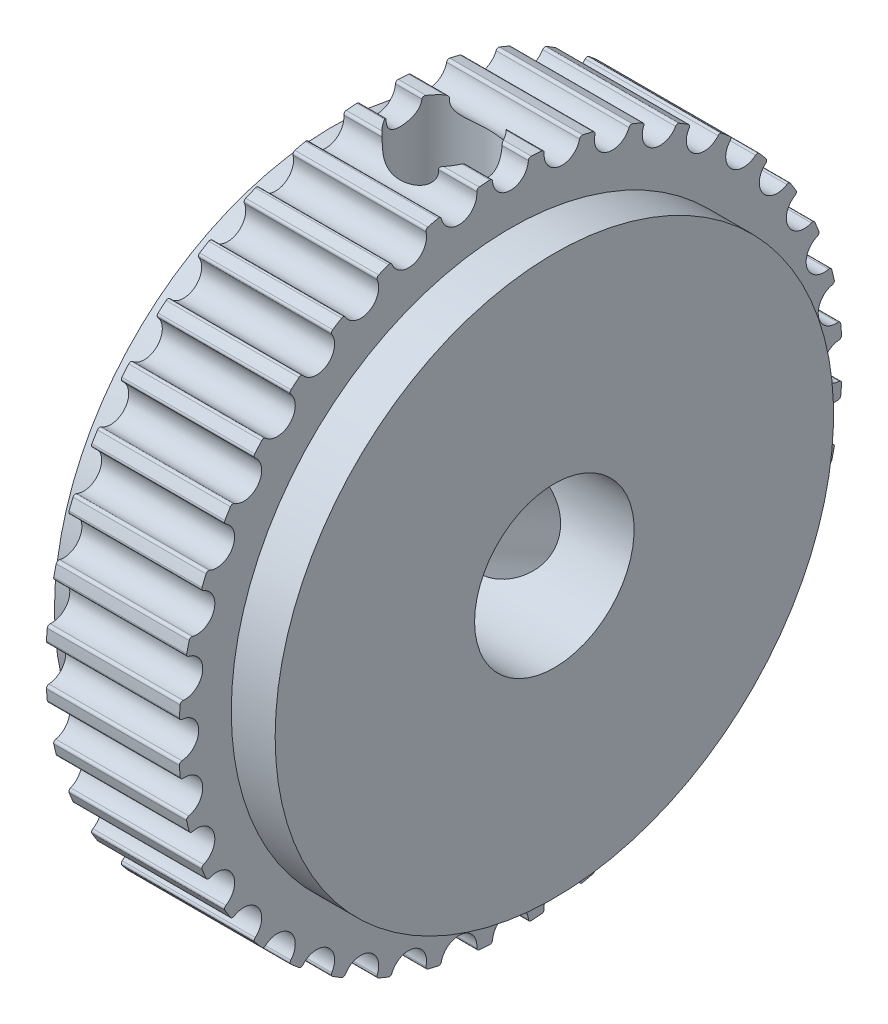
SolidWorks part; units mm, degrees
ref_plane "Front Plane" through (0, 0, 0) normal (0, 0, 1) x (1, 0, 0)
ref_plane "Top Plane" through (0, 0, 0) normal (0, 1, 0) x (1, 0, 0)
ref_plane "Right Plane" through (0, 0, 0) normal (1, 0, 0) x (0, 0, -1)
sketch "Sketch1" plane through (0, 0, 0) normal (0, 0, 1) x (1, 0, 0)
  line L0 (1.65, 12.73) -> (6.65, 12.73) construction
  line L1 (1.65, 12.475) -> (6.65, 12.475)
  line L2 (0, 10.5) -> (0, 3)
  line L4 (8.3, 10.5) -> (8.3, 3)
  line L5 (0, 3) -> (8.3, 3)
  line L6 (0, 0) -> (8.3, 0) construction
  line L8 (1.65, 10.5) -> (0, 10.5)
  line L9 (6.65, 10.5) -> (6.65, 12.475)
  line L10 (8.3, 10.5) -> (6.65, 10.5)
  line L13 (1.65, 10.5) -> (1.65, 12.475)
  dimension "D2" = 1.65
  dimension "D1" = 1.65
  dimension "O.D." = 24.95
  dimension "W" = 8.3
  dimension "E" = 21
  dimension "P.D." = 25.46
  dimension "A" = 5
  dimension "P" = 6
revolve "Revolve1" add sketch "Sketch1" angle 360 about L6
sketch "Sketch2" plane through (1.65, 0, 0) normal (1, 0, 0) x (0, 0, -1)
  line L0 (0, 0) -> (0, 12.475) construction
  circle A0 centre (0, 0) radius 12.475 construction
  circle A1 centre (0, 0) radius 12.475 construction
  arc A2 (0.6726, 12.4569) -> (-0.6726, 12.4569) centre (0, 0) ccw
  arc A3 (-0.6726, 12.4569) -> (0.6726, 12.4569) centre (0, 12.4) ccw
  circle A6 centre (0, 0) radius 11.725 construction
  circle A7 centre (0, 0) radius 12.729 construction
  dimension "MSM_3" = 0.675
  dimension "MSM_2" = 0.254
  dimension "MSM_1" = 0.75
extrude "Cut-Extrude1" cut sketch "Sketch2" along normal through all
fillet "Fillet1" radius 0.1 2 edges at (4.15, 12.4569, -0.6726) (4.15, 12.4569, 0.6726)
pattern_circular "CirPattern1" count 40 over 360 about axis through (0, 0, 0) along (1, 0, 0) of "Cut-Extrude1", "Fillet1"
ref_plane "Plane1" through (0, 12.475, 0) normal (0, 1, 0) x (1, 0, 0)
hole_wizard "Tapped Hole1" positions "Sketch4" profile "Sketch3" tap size "M4x0.7" standard "JIS"
sketch "Sketch4" plane through (-11.0915, 12.475, -15.1051) normal (0, 1, 0) x (1, 0, 0)
  line L0 (11.0915, -4.6051) -> (11.0915, -25.6051) construction
  line L1 (15.2415, -15.1051) -> (11.0915, -15.1051) construction
  point P0 (15.2415, -15.1051)
  dimension "D1" = 4.15
sketch "Sketch3" plane through (4.15, 12.475, 0) normal (1, 0, 0) x (0, 0, 1)
  line L0 (0, 0) -> (0, 9.475)
  line L1 (0, 9.475) -> (1.65, 9.475)
  line L2 (1.65, 9.475) -> (1.65, 0)
  line L5 (1.65, 0) -> (0, 0)
  line L11 (0, 0) -> (0, 9.475) construction
  dimension "Thru Tap Drill Dia." = 3.3
  dimension "Thru Tap Drill Depth" = 9.475
cosmetic thread "Hole Thread1" parameters "M"=4
pattern_circular "CirPattern2" count 2 every 120 about axis through (0, 0, 0) along (-1, 0, 0) of "Tapped Hole1"
hole_wizard "Tapped Hole2" [suppressed] positions "Sketch9" profile "Sketch8" tap size "M3x0.5" standard "JIS"
sketch "Sketch9" [suppressed] plane through (10.3, 8.8848, 0.534) normal (1, 0, 0) x (0, 0, -1)
  line L2 (0.534, -8.8848) -> (0.534, -16.8848) construction
  line L3 (0.534, -8.8848) -> (-6.3942, -4.8848) construction
  circle A0 centre (0.534, -8.8848) radius 8 construction
  point P0 (0.534, -16.8848)
  point P23 (-6.3942, -4.8848)
  point P24 (7.4622, -4.8848)
  dimension "QTC" = 16
  dimension "Angle_2" = 120
  dimension "Number" = 3
sketch "Sketch8" [suppressed] plane through (10.3, -8, 0) normal (0, 1, 0) x (0, 0, -1)
  line L0 (0, 0) -> (0, 9.2511)
  line L1 (0, 9.2511) -> (1.25, 8.5)
  line L2 (1.25, 8.5) -> (1.25, 0)
  line L5 (1.25, 0) -> (0, 0)
  line L10 (0, 9.2511) -> (-1.25, 8.5) construction
  line L11 (0, 0) -> (0, 9.2511) construction
  dimension "Tap Drill Dia." = 2.5
  dimension "Tap Drill Depth" = 8.5
  dimension "Drill Angle" = 118
cosmetic thread "Hole Thread2" [suppressed] parameters "Mx2"=6, "M"=3
cosmetic thread "Hole Thread3" [suppressed] parameters "Mx2"=6, "M"=3
cosmetic thread "Hole Thread4" [suppressed] parameters "Mx2"=6, "M"=3
hole_wizard "Tapped Hole3" [suppressed] positions "Sketch11" profile "Sketch10" tap size "M3x0.5" standard "JIS"
sketch "Sketch11" [suppressed] plane through (10.3, 6.1168, -5.003) normal (1, 0, 0) x (0, 0, -1)
  line L3 (-5.003, -6.1168) -> (-10.6598, -11.7737) construction
  line L4 (-5.003, -6.1168) -> (-10.6598, -0.46) construction
  line L5 (-5.003, 1.8832) -> (-5.003, -14.1168) construction
  circle A0 centre (-5.003, -6.1168) radius 8 construction
  point P22 (-10.6598, -11.7737)
  point P23 (6.0104, 6.0104)
  point P27 (-10.6598, -0.46)
  point P28 (0.6539, -0.46)
  point P29 (0.6539, -11.7737)
  dimension "QFC" = 16
  dimension "Angle_2" = 90
  dimension "Angle_1" = 45
  dimension "Number" = 4
sketch "Sketch10" [suppressed] plane through (10.3, -5.6569, 5.6569) normal (0, 1, 0) x (0, 0, -1)
  line L0 (0, 0) -> (0, 9.2511)
  line L1 (0, 9.2511) -> (1.25, 8.5)
  line L2 (1.25, 8.5) -> (1.25, 0)
  line L5 (1.25, 0) -> (0, 0)
  line L10 (0, 9.2511) -> (-1.25, 8.5) construction
  line L11 (0, 0) -> (0, 9.2511) construction
  dimension "Tap Drill Dia." = 2.5
  dimension "Tap Drill Depth" = 8.5
  dimension "Drill Angle" = 118
cosmetic thread "Hole Thread5" [suppressed] parameters "Mx2"=6, "M"=3
cosmetic thread "Hole Thread6" [suppressed] parameters "Mx2"=6, "M"=3
cosmetic thread "Hole Thread7" [suppressed] parameters "Mx2"=6, "M"=3
cosmetic thread "Hole Thread8" [suppressed] parameters "Mx2"=6, "M"=3
hole_wizard "Diameter Hole1" [suppressed] positions "Sketch15" profile "Sketch14" hole size "Ø4.0" standard "JIS"
sketch "Sketch15" [suppressed] plane through (0, 0, 0) normal (1, 0, 0) x (0, 0, -1)
  line L11 (0, 0) -> (0, -8) construction
  line L12 (0, 0) -> (-6.9282, 4) construction
  circle A2 centre (0, 0) radius 8 construction
  point P16 (0, -8)
  point P80 (-6.9282, 4)
  point P81 (6.9282, 4)
  dimension "D1" = 120
  dimension "KTC" = 16
  dimension "D2" = 3
sketch "Sketch14" [suppressed] plane through (0, -8, 0) normal (0, 1, 0) x (0, 0, 1)
  line L0 (0, 0) -> (0, 10.3)
  line L1 (0, 10.3) -> (2, 10.3)
  line L2 (2, 10.3) -> (2, 0)
  line L5 (2, 0) -> (0, 0)
  line L11 (0, 0) -> (0, 10.3) construction
  dimension "K" = 4
  dimension "Thru Hole Depth" = 10.3
hole_wizard "Diameter Hole2" [suppressed] positions "Sketch17" profile "Sketch16" hole size "Ø4.0" standard "JIS"
sketch "Sketch17" [suppressed] plane through (0, 0, 0) normal (1, 0, 0) x (0, 0, -1)
  line L18 (0, 0) -> (-5.6569, -5.6569) construction
  line L19 (0, 0) -> (-5.6569, 5.6569) construction
  line L20 (0, 8) -> (0, -8) construction
  circle A2 centre (0, 0) radius 8 construction
  point P104 (-5.6569, -5.6569)
  point P120 (-6.364, 6.364)
  point P146 (-5.6569, 5.6569)
  point P147 (5.6569, 5.6569)
  point P148 (5.6569, -5.6569)
  dimension "D1" = 90
  dimension "KFC" = 16
  dimension "D2" = 45
  dimension "D3" = 4
sketch "Sketch16" [suppressed] plane through (0, -5.6569, 5.6569) normal (0, 1, 0) x (0, 0, 1)
  line L0 (0, 0) -> (0, 10.3)
  line L1 (0, 10.3) -> (2, 10.3)
  line L2 (2, 10.3) -> (2, 0)
  line L5 (2, 0) -> (0, 0)
  line L11 (0, 0) -> (0, 10.3) construction
  dimension "K" = 4
  dimension "Thru Hole Depth" = 10.3
hole_wizard "CBORE for Socket Head Cap Screw1" [suppressed] positions "Sketch21" profile "Sketch20" counterbore size "M3" standard "JIS"
sketch "Sketch21" [suppressed] plane through (0, 0, 0) normal (-1, 0, 0) x (0, 0, 1)
  line L2 (0, 0) -> (0, -9.25) construction
  line L4 (0, 0) -> (8.0107, 4.625) construction
  circle A0 centre (0, 0) radius 9.25 construction
  circle A1 centre (8.0107, 4.625) radius 1.5 construction
  point P0 (0, -9.25)
  point P38 (-8.0107, 4.625)
  point P39 (8.0107, 4.625)
  dimension "ZTC" = 18.5
  dimension "D2" = 120
  dimension "D1" = 3
sketch "Sketch20" [suppressed] plane through (0, -9.25, 0) normal (0, 1, 0) x (0, 0, 1)
  line L0 (0, 0) -> (0, 10.3)
  line L1 (0, 10.3) -> (1.7, 10.3)
  line L3 (1.7, 10.3) -> (1.7, 3)
  line L4 (1.7, 3) -> (3.25, 3)
  line L5 (3.25, 3) -> (3.25, 0)
  line L7 (3.25, 0) -> (0, 0)
  line L11 (0, 0) -> (0, 10.3) construction
  dimension "D1_s" = 3.4
  dimension "Thru Hole Depth" = 10.3
  dimension "D2_s" = 6.5
  dimension "H_s" = 3
hole_wizard "CBORE for Socket Head Cap Screw2" [suppressed] positions "Sketch23" profile "Sketch22" counterbore size "M3" standard "JIS"
sketch "Sketch23" [suppressed] plane through (0, 0, 0) normal (-1, 0, 0) x (0, 0, 1)
  line L0 (0, 0) -> (0, 9.25) construction
  line L2 (6.5407, 6.5407) -> (0, 0) construction
  line L3 (0, 0) -> (6.5407, -6.5407) construction
  circle A0 centre (0, 0) radius 9.25 construction
  circle A1 centre (6.5407, 6.5407) radius 1.5 construction
  point P0 (6.5407, 6.5407)
  point P31 (6.5407, -6.5407)
  point P32 (-6.5407, -6.5407)
  point P33 (-6.5407, 6.5407)
  dimension "ZFC" = 18.5
  dimension "D2" = 45
  dimension "D3" = 90
  dimension "D1" = 4
sketch "Sketch22" [suppressed] plane through (0, 6.5407, 6.5407) normal (0, 1, 0) x (0, 0, 1)
  line L0 (0, 0) -> (0, 10.3)
  line L1 (0, 10.3) -> (1.75, 10.3)
  line L3 (1.75, 10.3) -> (1.75, 3.5)
  line L4 (1.75, 3.5) -> (3.25, 3.5)
  line L5 (3.25, 3.5) -> (3.25, 0)
  line L7 (3.25, 0) -> (0, 0)
  line L11 (0, 0) -> (0, 10.3) construction
  dimension "D1_s" = 3.5
  dimension "Thru Hole Depth" = 10.3
  dimension "D2_s" = 6.5
  dimension "H_s" = 3.5
equation "\"D1@Sketch4\" = \"W@Sketch1\" / 2"
equation "\"Plane dim\"= \"O.D.@Sketch1\" * 0.5"
equation "\"ZM\"=3.000000"
